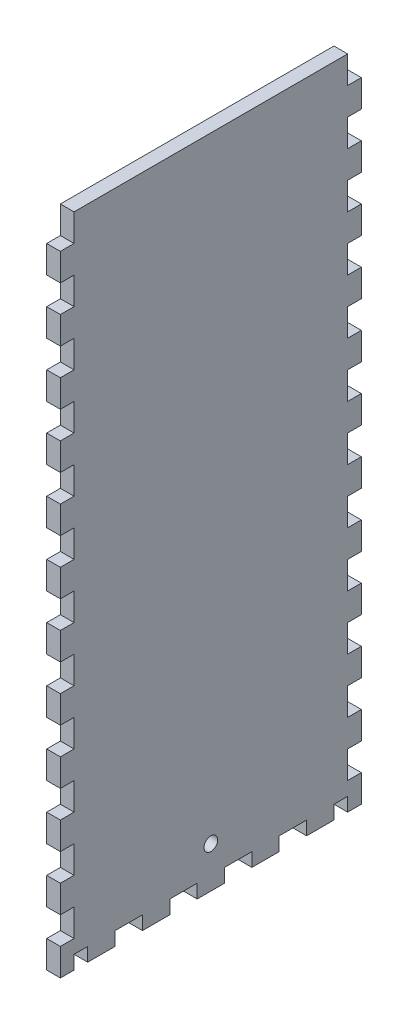
SolidWorks part; units mm, degrees
material "Acrylic (Medium-high impact)"
ref_plane "Front Plane" through (0, 0, 0) normal (0, 0, 1) x (1, 0, 0)
ref_plane "Top Plane" through (0, 0, 0) normal (0, 1, 0) x (1, 0, 0)
ref_plane "Right Plane" through (0, 0, 0) normal (1, 0, 0) x (0, 0, -1)
sketch "Sketch1" plane through (0, 0, 0) normal (0, 1, 0) x (1, 0, 0)
  line L1 (-136.525, 69.85) -> (136.525, 69.85)
  line L2 (-136.525, 69.85) -> (-136.525, -69.85)
  line L3 (-136.525, -69.85) -> (136.525, -69.85)
  line L4 (136.525, 69.85) -> (136.525, -69.85)
  point P4 (-136.525, 0)
  point P6 (0, 69.85)
  dimension "D1" = 139.7
  dimension "D2" = 273.05
extrude "Boss-Extrude1" add sketch "Sketch1" along normal blind 6.35
sketch "Sketch2" plane through (0, 6.35, 0) normal (0, 1, 0) x (1, 0, 0)
  line L0 (136.525, -69.85) -> (136.525, 69.85) construction
  line L1 (-136.525, 69.85) -> (136.525, 69.85)
  line L2 (-136.525, 69.85) -> (-136.525, -69.85)
  line L3 (-136.525, -69.85) -> (136.525, -69.85)
  line L4 (136.525, 69.85) -> (136.525, -69.85)
  line L5 (-136.525, -69.85) -> (136.525, -69.85) construction
  line L7 (-130.175, 63.5) -> (130.175, 63.5)
  line L8 (-130.175, 63.5) -> (-130.175, -63.5)
  line L9 (-130.175, -63.5) -> (130.175, -63.5)
  line L10 (130.175, 63.5) -> (130.175, -63.5)
  point P7 (-130.175, 0)
  point P14 (-136.525, 0)
  point P15 (0, -63.5)
  point P16 (0, -69.85)
  point P17 (130.175, 0)
  point P18 (136.525, 0)
  dimension "D1" = 6.35
  dimension "D2" = 6.35
extrude "Boss-Extrude2" add sketch "Sketch2" along normal blind 298.45
sketch "Sketch3" plane through (0, 0, 69.85) normal (0, 0, 1) x (1, 0, 0)
  line L0 (-25.273, 304.8) -> (-25.273, 0) construction
  line L2 (-130.175, 6.35) -> (130.175, 6.35) construction
  line L4 (-28.575, 283.21) -> (-28.575, 6.35)
  line L5 (-28.575, 6.35) -> (-21.971, 6.35)
  line L6 (-21.971, 292.354) -> (-21.971, 6.35)
  line L7 (-21.971, 292.354) -> (-41.529, 292.354)
  line L9 (-31.115, 285.75) -> (-41.529, 285.75)
  line L10 (-41.529, 292.354) -> (-41.529, 285.75)
  line L11 (-21.971, 101.6) -> (-9.271, 101.6) construction
  line L12 (-136.525, 0) -> (136.525, 0) construction
  line L13 (-12.446, 88.9) -> (-12.446, 101.6) construction
  line L14 (-15.621, 88.9) -> (-9.271, 88.9)
  line L15 (-15.621, 88.9) -> (-15.621, 71.9667)
  line L16 (-15.621, 71.9667) -> (-9.271, 71.9667)
  line L17 (-9.271, 88.9) -> (-9.271, 71.9667)
  line L18 (-15.621, 42.3333) -> (-9.271, 42.3333)
  line L19 (-15.621, 42.3333) -> (-15.621, 59.2667)
  line L20 (-15.621, 59.2667) -> (-9.271, 59.2667)
  line L21 (-9.271, 42.3333) -> (-9.271, 59.2667)
  line L26 (-15.621, 29.6333) -> (-9.271, 29.6333)
  line L27 (-15.621, 29.6333) -> (-15.621, 12.7)
  line L28 (-15.621, 12.7) -> (-9.271, 12.7)
  line L29 (-9.271, 29.6333) -> (-9.271, 12.7)
  line L30 (-12.446, 59.2667) -> (-12.446, 71.9667) construction
  line L31 (-12.446, 29.6333) -> (-12.446, 42.3333) construction
  line L32 (-12.446, 12.7) -> (-12.446, 0) construction
  line L33 (-136.525, 304.8) -> (136.525, 304.8) construction
  line L34 (-130.175, 304.8) -> (-130.175, 6.35) construction
  arc A0 (-28.575, 283.21) -> (-31.115, 285.75) centre (-31.115, 283.21) ccw
  point P5 (-25.273, 6.35)
  dimension "D5" = 2.54
  dimension "D1" = 6.604
  dimension "D2" = 12.954
  dimension "D3" = 6.604
  dimension "D4" = 286.004
  dimension "D6" = 101.6
  dimension "D7" = 12.7
  dimension "D8" = 12.7
  dimension "D9" = 6.35
  dimension "D10" = 101.6
extrude "Door Slot" cut sketch "Sketch3" against normal blind 12.7
sketch "Sketch4" plane through (0, 0, -63.5) normal (0, 0, 1) x (1, 0, 0)
  line L0 (-136.525, 304.8) -> (136.525, 304.8) construction
  line L1 (-47.879, 304.8) -> (-41.529, 304.8)
  line L2 (-47.879, 304.8) -> (-47.879, 6.35)
  line L3 (-47.879, 6.35) -> (-41.529, 6.35)
  line L4 (-41.529, 304.8) -> (-41.529, 6.35)
  line L5 (-18.796, 263.525) -> (-18.796, 247.65) construction
  line L6 (-41.529, 292.354) -> (-41.529, 285.75) construction
  line L7 (-21.971, 304.8) -> (-15.621, 304.8)
  line L8 (-21.971, 304.8) -> (-21.971, 6.35)
  line L9 (-21.971, 6.35) -> (-15.621, 6.35)
  line L10 (-15.621, 304.8) -> (-15.621, 6.35)
  line L11 (130.175, 6.35) -> (-130.175, 6.35) construction
  line L12 (-21.971, 6.35) -> (-21.971, 292.354) construction
  line L13 (-41.529, 304.8) -> (-47.879, 304.8)
  line L14 (-41.529, 304.8) -> (-41.529, 292.1)
  line L15 (-41.529, 292.1) -> (-47.879, 292.1)
  line L16 (-47.879, 304.8) -> (-47.879, 292.1)
  line L17 (-41.529, 276.225) -> (-47.879, 276.225)
  line L18 (-41.529, 276.225) -> (-41.529, 263.525)
  line L19 (-41.529, 263.525) -> (-47.879, 263.525)
  line L20 (-47.879, 276.225) -> (-47.879, 263.525)
  line L21 (-47.879, 6.35) -> (-41.529, 6.35)
  line L22 (-47.879, 6.35) -> (-47.879, 19.05)
  line L23 (-47.879, 19.05) -> (-41.529, 19.05)
  line L24 (-41.529, 6.35) -> (-41.529, 19.05)
  line L25 (-47.879, 34.925) -> (-41.529, 34.925)
  line L26 (-47.879, 34.925) -> (-47.879, 47.625)
  line L27 (-47.879, 47.625) -> (-41.529, 47.625)
  line L28 (-41.529, 34.925) -> (-41.529, 47.625)
  line L29 (-47.879, 92.075) -> (-41.529, 92.075)
  line L30 (-47.879, 92.075) -> (-47.879, 104.775)
  line L31 (-47.879, 104.775) -> (-41.529, 104.775)
  line L32 (-41.529, 92.075) -> (-41.529, 104.775)
  line L33 (-47.879, 149.225) -> (-41.529, 149.225)
  line L34 (-47.879, 149.225) -> (-47.879, 161.925)
  line L35 (-47.879, 161.925) -> (-41.529, 161.925)
  line L36 (-41.529, 149.225) -> (-41.529, 161.925)
  line L37 (-47.879, 177.8) -> (-41.529, 177.8)
  line L38 (-47.879, 177.8) -> (-47.879, 190.5)
  line L39 (-47.879, 190.5) -> (-41.529, 190.5)
  line L40 (-41.529, 177.8) -> (-41.529, 190.5)
  line L41 (-47.879, 206.375) -> (-41.529, 206.375)
  line L42 (-47.879, 206.375) -> (-47.879, 219.075)
  line L43 (-47.879, 219.075) -> (-41.529, 219.075)
  line L44 (-41.529, 206.375) -> (-41.529, 219.075)
  line L45 (-47.879, 234.95) -> (-41.529, 234.95)
  line L46 (-47.879, 234.95) -> (-47.879, 247.65)
  line L47 (-47.879, 247.65) -> (-41.529, 247.65)
  line L48 (-41.529, 234.95) -> (-41.529, 247.65)
  line L49 (-41.529, 133.35) -> (-47.879, 133.35)
  line L50 (-41.529, 133.35) -> (-41.529, 120.65)
  line L51 (-41.529, 120.65) -> (-47.879, 120.65)
  line L52 (-47.879, 133.35) -> (-47.879, 120.65)
  line L53 (-41.529, 76.2) -> (-47.879, 76.2)
  line L54 (-41.529, 76.2) -> (-41.529, 63.5)
  line L55 (-41.529, 63.5) -> (-47.879, 63.5)
  line L56 (-47.879, 76.2) -> (-47.879, 63.5)
  line L57 (-44.704, 304.8) -> (-44.704, 292.1) construction
  line L58 (-44.704, 292.1) -> (-44.704, 276.225) construction
  line L59 (-44.704, 276.225) -> (-44.704, 263.525) construction
  line L60 (-44.704, 247.65) -> (-44.704, 234.95) construction
  line L61 (-44.704, 234.95) -> (-44.704, 219.075) construction
  line L62 (-44.704, 219.075) -> (-44.704, 206.375) construction
  line L63 (-44.704, 206.375) -> (-44.704, 190.5) construction
  line L64 (-44.704, 190.5) -> (-44.704, 177.8) construction
  line L65 (-44.704, 177.8) -> (-44.704, 161.925) construction
  line L66 (-44.704, 161.925) -> (-44.704, 149.225) construction
  line L67 (-44.704, 133.35) -> (-44.704, 120.65) construction
  line L68 (-44.704, 120.65) -> (-44.704, 104.775) construction
  line L69 (-44.704, 104.775) -> (-44.704, 92.075) construction
  line L70 (-44.704, 92.075) -> (-44.704, 76.2) construction
  line L71 (-44.704, 76.2) -> (-44.704, 63.5) construction
  line L72 (-44.704, 63.5) -> (-44.704, 47.625) construction
  line L73 (-44.704, 47.625) -> (-44.704, 34.925) construction
  line L74 (-44.704, 34.925) -> (-44.704, 19.05) construction
  line L75 (-44.704, 19.05) -> (-44.704, 6.35) construction
  line L76 (-44.704, 149.225) -> (-44.704, 133.35) construction
  line L77 (-44.704, 263.525) -> (-44.704, 247.65) construction
  line L78 (-31.75, 304.8) -> (-31.75, 0) construction
  line L79 (136.525, 304.8) -> (-136.525, 304.8) construction
  line L80 (136.525, 0) -> (-136.525, 0) construction
  line L81 (-31.75, 8.3493) -> (-21.971, 8.3493) construction
  line L82 (-31.75, 8.3493) -> (-41.529, 8.3493) construction
  line L83 (-18.796, 149.225) -> (-18.796, 133.35) construction
  line L84 (-18.796, 19.05) -> (-18.796, 6.35) construction
  line L85 (-18.796, 34.925) -> (-18.796, 19.05) construction
  line L86 (-18.796, 47.625) -> (-18.796, 34.925) construction
  line L87 (-18.796, 63.5) -> (-18.796, 47.625) construction
  line L88 (-18.796, 76.2) -> (-18.796, 63.5) construction
  line L89 (-18.796, 92.075) -> (-18.796, 76.2) construction
  line L90 (-18.796, 104.775) -> (-18.796, 92.075) construction
  line L91 (-18.796, 120.65) -> (-18.796, 104.775) construction
  line L92 (-18.796, 133.35) -> (-18.796, 120.65) construction
  line L93 (-18.796, 161.925) -> (-18.796, 149.225) construction
  line L94 (-18.796, 177.8) -> (-18.796, 161.925) construction
  line L95 (-18.796, 190.5) -> (-18.796, 177.8) construction
  line L96 (-18.796, 206.375) -> (-18.796, 190.5) construction
  line L97 (-18.796, 219.075) -> (-18.796, 206.375) construction
  line L98 (-18.796, 234.95) -> (-18.796, 219.075) construction
  line L99 (-18.796, 247.65) -> (-18.796, 234.95) construction
  line L100 (-18.796, 276.225) -> (-18.796, 263.525) construction
  line L101 (-18.796, 292.1) -> (-18.796, 276.225) construction
  line L102 (-18.796, 304.8) -> (-18.796, 292.1) construction
  line L103 (-15.621, 76.2) -> (-15.621, 63.5)
  line L104 (-21.971, 63.5) -> (-15.621, 63.5)
  line L105 (-21.971, 76.2) -> (-21.971, 63.5)
  line L106 (-21.971, 76.2) -> (-15.621, 76.2)
  line L107 (-15.621, 133.35) -> (-15.621, 120.65)
  line L108 (-21.971, 120.65) -> (-15.621, 120.65)
  line L109 (-21.971, 133.35) -> (-21.971, 120.65)
  line L110 (-21.971, 133.35) -> (-15.621, 133.35)
  line L111 (-21.971, 234.95) -> (-21.971, 247.65)
  line L112 (-15.621, 247.65) -> (-21.971, 247.65)
  line L113 (-15.621, 234.95) -> (-15.621, 247.65)
  line L114 (-15.621, 234.95) -> (-21.971, 234.95)
  line L115 (-21.971, 206.375) -> (-21.971, 219.075)
  line L116 (-15.621, 219.075) -> (-21.971, 219.075)
  line L117 (-15.621, 206.375) -> (-15.621, 219.075)
  line L118 (-15.621, 206.375) -> (-21.971, 206.375)
  line L119 (-21.971, 177.8) -> (-21.971, 190.5)
  line L120 (-15.621, 190.5) -> (-21.971, 190.5)
  line L121 (-15.621, 177.8) -> (-15.621, 190.5)
  line L122 (-15.621, 177.8) -> (-21.971, 177.8)
  line L123 (-21.971, 149.225) -> (-21.971, 161.925)
  line L124 (-15.621, 161.925) -> (-21.971, 161.925)
  line L125 (-15.621, 149.225) -> (-15.621, 161.925)
  line L126 (-15.621, 149.225) -> (-21.971, 149.225)
  line L127 (-21.971, 92.075) -> (-21.971, 104.775)
  line L128 (-15.621, 104.775) -> (-21.971, 104.775)
  line L129 (-15.621, 92.075) -> (-15.621, 104.775)
  line L130 (-15.621, 92.075) -> (-21.971, 92.075)
  line L131 (-21.971, 34.925) -> (-21.971, 47.625)
  line L132 (-15.621, 47.625) -> (-21.971, 47.625)
  line L133 (-15.621, 34.925) -> (-15.621, 47.625)
  line L134 (-15.621, 34.925) -> (-21.971, 34.925)
  line L135 (-21.971, 6.35) -> (-21.971, 19.05)
  line L136 (-15.621, 19.05) -> (-21.971, 19.05)
  line L137 (-15.621, 6.35) -> (-15.621, 19.05)
  line L138 (-15.621, 6.35) -> (-21.971, 6.35)
  line L139 (-15.621, 276.225) -> (-15.621, 263.525)
  line L140 (-21.971, 263.525) -> (-15.621, 263.525)
  line L141 (-21.971, 276.225) -> (-21.971, 263.525)
  line L142 (-21.971, 276.225) -> (-15.621, 276.225)
  line L143 (-15.621, 304.8) -> (-15.621, 292.1)
  line L144 (-21.971, 292.1) -> (-15.621, 292.1)
  line L145 (-21.971, 304.8) -> (-21.971, 292.1)
  line L146 (-21.971, 304.8) -> (-15.621, 304.8)
  line L147 (-21.971, 304.8) -> (-21.971, 6.35)
  line L148 (-15.621, 6.35) -> (-21.971, 6.35)
  line L149 (-15.621, 304.8) -> (-15.621, 6.35)
  line L150 (-15.621, 304.8) -> (-21.971, 304.8)
  point P14 (-41.529, 289.052)
  dimension "D1" = 6.35
  dimension "D2" = 12.7
extrude "Door Guide Holes" cut sketch "Sketch4" against normal up to next contours L17 L4 L15 L2 | L2 L47 L4 L19 | L45 L2 L43 L4 | L41 L2 L39 L4 | L37 L2 L35 L4 | L49 L4 L33 L2 | L4 L51 L2 L31 | L53 L4 L29 L2 | L4 L55 L2 L27 | L25 L2 L23 L4
ref_plane "Plane1" through (-31.75, 0, 0) normal (-1, 0, 0) x (0, 0, 1)
mirror "Mirror1" about plane through (-31.75, 0, 0) normal (-1, 0, 0) of "Door Guide Holes"
sketch "Lever Holes" plane through (0, 0, 69.85) normal (0, 0, 1) x (1, 0, 0)
  line L0 (49.276, 31.75) -> (58.928, 31.75)
  line L1 (49.276, 31.75) -> (49.276, 25.4)
  line L2 (49.276, 25.4) -> (58.928, 25.4)
  line L3 (58.928, 31.75) -> (58.928, 25.4)
  line L4 (36.1315, 19.05) -> (42.4815, 19.05)
  line L5 (36.1315, 19.05) -> (36.1315, 12.7)
  line L6 (36.1315, 12.7) -> (42.4815, 12.7)
  line L7 (42.4815, 19.05) -> (42.4815, 12.7)
  line L8 (65.7225, 19.05) -> (72.0725, 19.05)
  line L9 (65.7225, 19.05) -> (65.7225, 12.7)
  line L10 (65.7225, 12.7) -> (72.0725, 12.7)
  line L11 (72.0725, 19.05) -> (72.0725, 12.7)
  line L12 (42.4815, 15.875) -> (65.7225, 15.875) construction
  line L13 (-136.525, 0) -> (136.525, 0) construction
  line L14 (-21.971, 6.35) -> (130.175, 6.35) construction
  line L15 (130.175, 6.35) -> (-130.175, 6.35) construction
  point P12 (54.102, 15.875)
  point P13 (54.102, 25.4)
  point P24 (54.102, 6.35)
  dimension "D1" = 9.652
  dimension "D2" = 6.35
  dimension "D3" = 6.35
  dimension "D4" = 6.35
  dimension "D5" = 23.241
  dimension "D6" = 25.4
  dimension "D7" = 12.7
extrude "Cut-Extrude1" cut sketch "Lever Holes" against normal through all
sketch "Sketch7" plane through (136.525, 0, 0) normal (1, 0, 0) x (0, 0, -1)
  line L0 (-37.211, 92.583) -> (37.211, 92.583)
  line L1 (-37.211, 92.583) -> (-37.211, 18.161)
  line L2 (-37.211, 18.161) -> (37.211, 18.161)
  line L3 (37.211, 92.583) -> (37.211, 18.161)
  line L4 (-69.85, 0) -> (69.85, 0) construction
  circle A0 centre (0, 55.372) radius 26.9875
  circle A1 centre (-37.211, 92.583) radius 3.175
  circle A2 centre (37.211, 92.583) radius 3.175
  circle A3 centre (-37.211, 18.161) radius 3.175
  circle A4 centre (37.211, 18.161) radius 3.175
  point P9 (0, 18.161)
  point P10 (-37.211, 55.372)
  dimension "D3" = 53.975
  dimension "D4" = 6.35
  dimension "D1" = 74.422
  dimension "D2" = 55.372
extrude "Cut-Extrude2" cut sketch "Sketch7" against normal up to next contours A0 | L0 A1 L1 | L1 A1 L0 | L3 A2 L0 | L0 A2 L3 | L2 A3 L1 | L1 A3 L2 | L2 A4 L3 | L3 A4 L2
sketch "Sketch8" plane through (-136.525, 0, 0) normal (-1, 0, 0) x (0, 0, 1)
  line L0 (-69.85, 0) -> (69.85, 0) construction
  circle A0 centre (0, 19.05) radius 3.175
  point P6 (0, 0)
  dimension "D1" = 6.35
  dimension "D2" = 19.05
extrude "Cut-Extrude3" cut sketch "Sketch8" against normal up to next
sketch "Bottom" plane through (0, 0, 0) normal (0, -1, 0) x (1, 0, 0)
  line L0 (-130.175, 63.5) -> (130.175, 63.5) construction
  line L1 (-136.525, 69.85) -> (-122.1539, 69.85)
  line L2 (-136.525, 69.85) -> (-136.525, 63.5)
  line L3 (-136.525, 63.5) -> (-122.1539, 63.5)
  line L4 (-122.1539, 69.85) -> (-122.1539, 63.5)
  line L5 (-122.1539, 69.85) -> (-107.7829, 69.85)
  line L6 (-122.1539, 69.85) -> (-122.1539, 63.5)
  line L7 (-122.1539, 63.5) -> (-107.7829, 63.5)
  line L8 (-107.7829, 69.85) -> (-107.7829, 63.5)
  line L9 (-107.7829, 69.85) -> (-93.4118, 69.85)
  line L10 (-107.7829, 69.85) -> (-107.7829, 63.5)
  line L11 (-107.7829, 63.5) -> (-93.4118, 63.5)
  line L12 (-93.4118, 69.85) -> (-93.4118, 63.5)
  line L13 (-93.4118, 69.85) -> (-79.0408, 69.85)
  line L14 (-93.4118, 69.85) -> (-93.4118, 63.5)
  line L15 (-93.4118, 63.5) -> (-79.0408, 63.5)
  line L16 (-79.0408, 69.85) -> (-79.0408, 63.5)
  line L17 (-136.525, 69.85) -> (136.525, 69.85) construction
  line L18 (-41.529, 63.5) -> (-21.971, 63.5) construction
  line L19 (-79.0408, 69.85) -> (-64.6697, 69.85)
  line L20 (-79.0408, 69.85) -> (-79.0408, 63.5)
  line L21 (-79.0408, 63.5) -> (-64.6697, 63.5)
  line L22 (-64.6697, 69.85) -> (-64.6697, 63.5)
  line L23 (-64.6697, 69.85) -> (-50.2987, 69.85)
  line L24 (-64.6697, 69.85) -> (-64.6697, 63.5)
  line L25 (-64.6697, 63.5) -> (-50.2987, 63.5)
  line L26 (-50.2987, 69.85) -> (-50.2987, 63.5)
  line L27 (-50.2987, 69.85) -> (-35.9276, 69.85)
  line L28 (-50.2987, 69.85) -> (-50.2987, 63.5)
  line L29 (-50.2987, 63.5) -> (-35.9276, 63.5)
  line L30 (-35.9276, 69.85) -> (-35.9276, 63.5)
  line L31 (-35.9276, 69.85) -> (-21.5566, 69.85)
  line L32 (-35.9276, 69.85) -> (-35.9276, 63.5)
  line L33 (-35.9276, 63.5) -> (-21.5566, 63.5)
  line L34 (-21.5566, 69.85) -> (-21.5566, 63.5)
  line L36 (-21.5566, 69.85) -> (-7.1855, 69.85)
  line L37 (-21.5566, 69.85) -> (-21.5566, 63.5)
  line L38 (-21.5566, 63.5) -> (-7.1855, 63.5)
  line L39 (-7.1855, 69.85) -> (-7.1855, 63.5)
  line L40 (-7.1855, 69.85) -> (7.1855, 69.85)
  line L41 (-7.1855, 69.85) -> (-7.1855, 63.5)
  line L42 (-7.1855, 63.5) -> (7.1855, 63.5)
  line L43 (7.1855, 69.85) -> (7.1855, 63.5)
  line L44 (7.1855, 69.85) -> (21.5566, 69.85)
  line L45 (7.1855, 69.85) -> (7.1855, 63.5)
  line L46 (7.1855, 63.5) -> (21.5566, 63.5)
  line L47 (21.5566, 69.85) -> (21.5566, 63.5)
  line L48 (21.5566, 69.85) -> (35.9276, 69.85)
  line L49 (21.5566, 69.85) -> (21.5566, 63.5)
  line L50 (21.5566, 63.5) -> (35.9276, 63.5)
  line L51 (35.9276, 69.85) -> (35.9276, 63.5)
  line L52 (35.9276, 69.85) -> (50.2987, 69.85)
  line L53 (35.9276, 69.85) -> (35.9276, 63.5)
  line L54 (35.9276, 63.5) -> (50.2987, 63.5)
  line L55 (50.2987, 69.85) -> (50.2987, 63.5)
  line L56 (50.2987, 69.85) -> (64.6697, 69.85)
  line L57 (50.2987, 69.85) -> (50.2987, 63.5)
  line L58 (50.2987, 63.5) -> (64.6697, 63.5)
  line L59 (64.6697, 69.85) -> (64.6697, 63.5)
  line L60 (64.6697, 69.85) -> (79.0408, 69.85)
  line L61 (64.6697, 69.85) -> (64.6697, 63.5)
  line L62 (64.6697, 63.5) -> (79.0408, 63.5)
  line L63 (79.0408, 69.85) -> (79.0408, 63.5)
  line L64 (79.0408, 69.85) -> (93.4118, 69.85)
  line L65 (79.0408, 69.85) -> (79.0408, 63.5)
  line L66 (79.0408, 63.5) -> (93.4118, 63.5)
  line L67 (93.4118, 69.85) -> (93.4118, 63.5)
  line L68 (93.4118, 69.85) -> (107.7829, 69.85)
  line L69 (93.4118, 69.85) -> (93.4118, 63.5)
  line L70 (93.4118, 63.5) -> (107.7829, 63.5)
  line L71 (107.7829, 69.85) -> (107.7829, 63.5)
  line L72 (107.7829, 69.85) -> (122.1539, 69.85)
  line L73 (107.7829, 69.85) -> (107.7829, 63.5)
  line L74 (107.7829, 63.5) -> (122.1539, 63.5)
  line L75 (122.1539, 69.85) -> (122.1539, 63.5)
  line L76 (-130.175, -63.5) -> (-130.175, 63.5) construction
  line L77 (-136.525, 69.85) -> (-130.175, 69.85)
  line L78 (-136.525, 69.85) -> (-136.525, 57.15)
  line L79 (-136.525, 57.15) -> (-130.175, 57.15)
  line L80 (-130.175, 69.85) -> (-130.175, 57.15)
  line L82 (-136.525, 57.15) -> (-130.175, 57.15)
  line L83 (-136.525, 57.15) -> (-136.525, 44.45)
  line L84 (-136.525, 44.45) -> (-130.175, 44.45)
  line L85 (-130.175, 57.15) -> (-130.175, 44.45)
  line L86 (-136.525, 44.45) -> (-130.175, 44.45)
  line L87 (-136.525, 44.45) -> (-136.525, 31.75)
  line L88 (-136.525, 31.75) -> (-130.175, 31.75)
  line L89 (-130.175, 44.45) -> (-130.175, 31.75)
  line L90 (-136.525, 31.75) -> (-130.175, 31.75)
  line L91 (-136.525, 31.75) -> (-136.525, 19.05)
  line L92 (-136.525, 19.05) -> (-130.175, 19.05)
  line L93 (-130.175, 31.75) -> (-130.175, 19.05)
  line L94 (-136.525, 19.05) -> (-130.175, 19.05)
  line L95 (-136.525, 19.05) -> (-136.525, 6.35)
  line L96 (-136.525, 6.35) -> (-130.175, 6.35)
  line L97 (-130.175, 19.05) -> (-130.175, 6.35)
  line L98 (-136.525, 6.35) -> (-130.175, 6.35)
  line L99 (-136.525, 6.35) -> (-136.525, -6.35)
  line L100 (-136.525, -6.35) -> (-130.175, -6.35)
  line L101 (-130.175, 6.35) -> (-130.175, -6.35)
  line L102 (-136.525, -6.35) -> (-130.175, -6.35)
  line L103 (-136.525, -6.35) -> (-136.525, -19.05)
  line L104 (-136.525, -19.05) -> (-130.175, -19.05)
  line L105 (-130.175, -6.35) -> (-130.175, -19.05)
  line L106 (-136.525, -19.05) -> (-130.175, -19.05)
  line L107 (-136.525, -19.05) -> (-136.525, -31.75)
  line L108 (-136.525, -31.75) -> (-130.175, -31.75)
  line L109 (-130.175, -19.05) -> (-130.175, -31.75)
  line L110 (-136.525, -31.75) -> (-130.175, -31.75)
  line L111 (-136.525, -31.75) -> (-136.525, -44.45)
  line L112 (-136.525, -44.45) -> (-130.175, -44.45)
  line L113 (-130.175, -31.75) -> (-130.175, -44.45)
  line L114 (-136.525, -44.45) -> (-130.175, -44.45)
  line L115 (-136.525, -44.45) -> (-136.525, -57.15)
  line L116 (-136.525, -57.15) -> (-130.175, -57.15)
  line L117 (-130.175, -44.45) -> (-130.175, -57.15)
  line L118 (136.525, 69.85) -> (136.525, -69.85) construction
  line L119 (122.1539, 69.85) -> (136.525, 69.85)
  line L120 (122.1539, 69.85) -> (122.1539, 63.5)
  line L121 (122.1539, 63.5) -> (136.525, 63.5)
  line L122 (136.525, 69.85) -> (136.525, 63.5)
  line L123 (136.525, -69.85) -> (-136.525, -69.85) construction
  line L124 (-136.525, -57.15) -> (-130.175, -57.15)
  line L125 (-136.525, -57.15) -> (-136.525, -69.85)
  line L126 (-136.525, -69.85) -> (-130.175, -69.85)
  line L127 (-130.175, -57.15) -> (-130.175, -69.85)
  line L128 (150.1775, 0) -> (-150.1775, 0) construction
  line L129 (136.525, -69.85) -> (136.525, -63.5)
  line L130 (122.1539, -63.5) -> (136.525, -63.5)
  line L131 (122.1539, -69.85) -> (136.525, -69.85)
  line L132 (122.1539, -69.85) -> (122.1539, -63.5)
  line L133 (107.7829, -63.5) -> (122.1539, -63.5)
  line L134 (107.7829, -69.85) -> (122.1539, -69.85)
  line L135 (107.7829, -69.85) -> (107.7829, -63.5)
  line L136 (93.4118, -63.5) -> (107.7829, -63.5)
  line L137 (93.4118, -69.85) -> (107.7829, -69.85)
  line L138 (93.4118, -69.85) -> (93.4118, -63.5)
  line L139 (79.0408, -63.5) -> (93.4118, -63.5)
  line L140 (79.0408, -69.85) -> (93.4118, -69.85)
  line L141 (79.0408, -69.85) -> (79.0408, -63.5)
  line L142 (64.6697, -63.5) -> (79.0408, -63.5)
  line L143 (64.6697, -69.85) -> (79.0408, -69.85)
  line L144 (50.2987, -63.5) -> (64.6697, -63.5)
  line L145 (64.6697, -69.85) -> (64.6697, -63.5)
  line L146 (50.2987, -69.85) -> (64.6697, -69.85)
  line L147 (50.2987, -69.85) -> (50.2987, -63.5)
  line L148 (35.9276, -63.5) -> (50.2987, -63.5)
  line L149 (35.9276, -69.85) -> (50.2987, -69.85)
  line L150 (35.9276, -69.85) -> (35.9276, -63.5)
  line L151 (21.5566, -63.5) -> (35.9276, -63.5)
  line L152 (21.5566, -69.85) -> (35.9276, -69.85)
  line L153 (21.5566, -69.85) -> (21.5566, -63.5)
  line L154 (7.1855, -69.85) -> (21.5566, -69.85)
  line L155 (7.1855, -63.5) -> (21.5566, -63.5)
  line L156 (7.1855, -69.85) -> (7.1855, -63.5)
  line L157 (-7.1855, -63.5) -> (7.1855, -63.5)
  line L158 (-7.1855, -69.85) -> (7.1855, -69.85)
  line L159 (-21.5566, -63.5) -> (-7.1855, -63.5)
  line L160 (-7.1855, -69.85) -> (-7.1855, -63.5)
  line L161 (-21.5566, -69.85) -> (-7.1855, -69.85)
  line L162 (-21.5566, -69.85) -> (-21.5566, -63.5)
  line L163 (-35.9276, -63.5) -> (-21.5566, -63.5)
  line L164 (-35.9276, -69.85) -> (-21.5566, -69.85)
  line L165 (-35.9276, -69.85) -> (-35.9276, -63.5)
  line L166 (-50.2987, -63.5) -> (-35.9276, -63.5)
  line L167 (-50.2987, -69.85) -> (-35.9276, -69.85)
  line L168 (-50.2987, -69.85) -> (-50.2987, -63.5)
  line L169 (-64.6697, -69.85) -> (-50.2987, -69.85)
  line L170 (-64.6697, -63.5) -> (-50.2987, -63.5)
  line L171 (-79.0408, -63.5) -> (-64.6697, -63.5)
  line L172 (-64.6697, -69.85) -> (-64.6697, -63.5)
  line L173 (-79.0408, -69.85) -> (-64.6697, -69.85)
  line L174 (-93.4118, -69.85) -> (-79.0408, -69.85)
  line L175 (-93.4118, -63.5) -> (-79.0408, -63.5)
  line L176 (-79.0408, -69.85) -> (-79.0408, -63.5)
  line L177 (-107.7829, -69.85) -> (-107.7829, -63.5)
  line L178 (-107.7829, -69.85) -> (-93.4118, -69.85)
  line L179 (-93.4118, -69.85) -> (-93.4118, -63.5)
  line L180 (-107.7829, -63.5) -> (-93.4118, -63.5)
  line L181 (-122.1539, -63.5) -> (-107.7829, -63.5)
  line L182 (-122.1539, -69.85) -> (-107.7829, -69.85)
  line L183 (-122.1539, -69.85) -> (-122.1539, -63.5)
  line L184 (-136.525, -69.85) -> (-122.1539, -69.85)
  line L185 (-136.525, -69.85) -> (-136.525, -63.5)
  line L186 (-136.525, -63.5) -> (-122.1539, -63.5)
  line L187 (0, -76.835) -> (0, 76.835) construction
  line L188 (136.525, -69.85) -> (130.175, -69.85)
  line L189 (130.175, -57.15) -> (130.175, -69.85)
  line L190 (136.525, -57.15) -> (136.525, -69.85)
  line L191 (136.525, -57.15) -> (130.175, -57.15)
  line L192 (130.175, -44.45) -> (130.175, -57.15)
  line L193 (136.525, -44.45) -> (136.525, -57.15)
  line L194 (136.525, -44.45) -> (130.175, -44.45)
  line L195 (130.175, -31.75) -> (130.175, -44.45)
  line L196 (136.525, -31.75) -> (136.525, -44.45)
  line L197 (136.525, -31.75) -> (130.175, -31.75)
  line L198 (136.525, -19.05) -> (136.525, -31.75)
  line L199 (130.175, -19.05) -> (130.175, -31.75)
  line L200 (130.175, -6.35) -> (130.175, -19.05)
  line L201 (136.525, -6.35) -> (136.525, -19.05)
  line L202 (136.525, -19.05) -> (130.175, -19.05)
  line L203 (136.525, -6.35) -> (130.175, -6.35)
  line L204 (130.175, 6.35) -> (130.175, -6.35)
  line L205 (136.525, 6.35) -> (136.525, -6.35)
  line L206 (136.525, 6.35) -> (130.175, 6.35)
  line L207 (130.175, 19.05) -> (130.175, 6.35)
  line L208 (136.525, 19.05) -> (136.525, 6.35)
  line L209 (136.525, 19.05) -> (130.175, 19.05)
  line L210 (136.525, 31.75) -> (130.175, 31.75)
  line L211 (136.525, 44.45) -> (130.175, 44.45)
  line L212 (136.525, 57.15) -> (130.175, 57.15)
  line L213 (130.175, 31.75) -> (130.175, 19.05)
  line L214 (136.525, 31.75) -> (136.525, 19.05)
  line L215 (130.175, 44.45) -> (130.175, 31.75)
  line L216 (136.525, 44.45) -> (136.525, 31.75)
  line L217 (130.175, 57.15) -> (130.175, 44.45)
  line L218 (136.525, 57.15) -> (136.525, 44.45)
  line L219 (130.175, 69.85) -> (130.175, 57.15)
  line L220 (136.525, 69.85) -> (136.525, 57.15)
sketch "Front/Back" plane through (0, 0, 69.85) normal (0, 0, 1) x (1, 0, 0)
  line L0 (-130.175, 6.35) -> (-28.575, 6.35) construction
  line L1 (-136.525, 0) -> (-122.1539, 0)
  line L2 (-136.525, 0) -> (-136.525, 6.35)
  line L3 (-136.525, 6.35) -> (-122.1539, 6.35)
  line L4 (-122.1539, 0) -> (-122.1539, 6.35)
  line L5 (-136.525, 0) -> (136.525, 0) construction
  line L6 (-107.7829, 0) -> (-93.4118, 0) construction
  line L7 (-122.1539, 6.35) -> (-107.7829, 6.35)
  line L8 (-122.1539, 6.35) -> (-122.1539, 0)
  line L9 (-122.1539, 0) -> (-107.7829, 0)
  line L10 (-107.7829, 6.35) -> (-107.7829, 0)
  line L11 (-79.0408, 0) -> (-64.6697, 0) construction
  line L12 (-107.7829, 6.35) -> (-93.4118, 6.35)
  line L13 (-107.7829, 6.35) -> (-107.7829, 0)
  line L14 (-107.7829, 0) -> (-93.4118, 0)
  line L15 (-93.4118, 6.35) -> (-93.4118, 0)
  line L16 (-93.4118, 6.35) -> (-79.0408, 6.35)
  line L17 (-93.4118, 6.35) -> (-93.4118, 0)
  line L18 (-93.4118, 0) -> (-79.0408, 0)
  line L19 (-79.0408, 6.35) -> (-79.0408, 0)
  line L20 (-64.6697, 0) -> (-50.2987, 0) construction
  line L21 (-79.0408, 6.35) -> (-64.6697, 6.35)
  line L22 (-79.0408, 6.35) -> (-79.0408, 0)
  line L23 (-79.0408, 0) -> (-64.6697, 0)
  line L24 (-64.6697, 6.35) -> (-64.6697, 0)
  line L25 (-64.6697, 6.35) -> (-50.2987, 6.35)
  line L26 (-64.6697, 6.35) -> (-64.6697, 0)
  line L27 (-64.6697, 0) -> (-50.2987, 0)
  line L28 (-50.2987, 6.35) -> (-50.2987, 0)
  line L29 (-50.2987, 0) -> (-35.9276, 0) construction
  line L30 (-50.2987, 6.35) -> (-35.9276, 6.35)
  line L31 (-50.2987, 6.35) -> (-50.2987, 0)
  line L32 (-50.2987, 0) -> (-35.9276, 0)
  line L33 (-35.9276, 6.35) -> (-35.9276, 0)
  line L34 (-21.5566, 0) -> (-7.1855, 0) construction
  line L35 (-35.9276, 6.35) -> (-21.5566, 6.35)
  line L36 (-35.9276, 6.35) -> (-35.9276, 0)
  line L37 (-35.9276, 0) -> (-21.5566, 0)
  line L38 (-21.5566, 6.35) -> (-21.5566, 0)
  line L39 (7.1855, 0) -> (21.5566, 0) construction
  line L40 (-21.5566, 6.35) -> (-7.1855, 6.35)
  line L41 (-21.5566, 6.35) -> (-21.5566, 0)
  line L42 (-21.5566, 0) -> (-7.1855, 0)
  line L43 (-7.1855, 6.35) -> (-7.1855, 0)
  line L44 (-7.1855, 6.35) -> (7.1855, 6.35)
  line L45 (-7.1855, 6.35) -> (-7.1855, 0)
  line L46 (-7.1855, 0) -> (7.1855, 0)
  line L47 (7.1855, 6.35) -> (7.1855, 0)
  line L48 (7.1855, 0) -> (21.5566, 0) construction
  line L49 (35.9276, 0) -> (50.2987, 0) construction
  line L50 (7.1855, 6.35) -> (21.5566, 6.35)
  line L51 (7.1855, 6.35) -> (7.1855, 0)
  line L52 (7.1855, 0) -> (21.5566, 0)
  line L53 (21.5566, 6.35) -> (21.5566, 0)
  line L54 (21.5566, 6.35) -> (35.9276, 6.35)
  line L55 (21.5566, 6.35) -> (21.5566, 0)
  line L56 (21.5566, 0) -> (35.9276, 0)
  line L57 (35.9276, 6.35) -> (35.9276, 0)
  line L58 (64.6697, 0) -> (79.0408, 0) construction
  line L59 (35.9276, 6.35) -> (50.2987, 6.35)
  line L60 (35.9276, 6.35) -> (35.9276, 0)
  line L61 (35.9276, 0) -> (50.2987, 0)
  line L62 (50.2987, 6.35) -> (50.2987, 0)
  line L63 (50.2987, 6.35) -> (64.6697, 6.35)
  line L64 (50.2987, 6.35) -> (50.2987, 0)
  line L65 (50.2987, 0) -> (64.6697, 0)
  line L66 (64.6697, 6.35) -> (64.6697, 0)
  line L67 (50.2987, 0) -> (64.6697, 0) construction
  line L68 (93.4118, 0) -> (107.7829, 0) construction
  line L69 (64.6697, 6.35) -> (79.0408, 6.35)
  line L70 (64.6697, 6.35) -> (64.6697, 0)
  line L71 (64.6697, 0) -> (79.0408, 0)
  line L72 (79.0408, 6.35) -> (79.0408, 0)
  line L73 (79.0408, 6.35) -> (93.4118, 6.35)
  line L74 (79.0408, 6.35) -> (79.0408, 0)
  line L75 (79.0408, 0) -> (93.4118, 0)
  line L76 (93.4118, 6.35) -> (93.4118, 0)
  line L77 (107.7829, 0) -> (122.1539, 0) construction
  line L78 (93.4118, 6.35) -> (107.7829, 6.35)
  line L79 (93.4118, 6.35) -> (93.4118, 0)
  line L80 (93.4118, 0) -> (107.7829, 0)
  line L81 (107.7829, 6.35) -> (107.7829, 0)
  line L82 (107.7829, 0) -> (122.1539, 0) construction
  line L84 (107.7829, 6.35) -> (122.1539, 6.35)
  line L85 (107.7829, 6.35) -> (107.7829, 0)
  line L86 (107.7829, 0) -> (122.1539, 0)
  line L87 (122.1539, 6.35) -> (122.1539, 0)
  line L88 (122.1539, 6.35) -> (136.525, 6.35)
  line L89 (122.1539, 6.35) -> (122.1539, 0)
  line L90 (122.1539, 0) -> (136.525, 0)
  line L91 (136.525, 6.35) -> (136.525, 0)
  line L92 (-130.175, 304.8) -> (-130.175, 6.35) construction
  line L93 (-136.525, 0) -> (-130.175, 0)
  line L94 (-136.525, 0) -> (-136.525, 12.7)
  line L95 (-136.525, 12.7) -> (-130.175, 12.7)
  line L96 (-130.175, 0) -> (-130.175, 12.7)
  line L97 (-136.525, 304.8) -> (-136.525, 0) construction
  line L98 (-136.525, 12.7) -> (-130.175, 12.7)
  line L99 (-136.525, 12.7) -> (-136.525, 25.4)
  line L100 (-136.525, 25.4) -> (-130.175, 25.4)
  line L101 (-130.175, 12.7) -> (-130.175, 25.4)
  line L102 (-136.525, 25.4) -> (-130.175, 25.4)
  line L103 (-136.525, 25.4) -> (-136.525, 38.1)
  line L104 (-136.525, 38.1) -> (-130.175, 38.1)
  line L105 (-130.175, 25.4) -> (-130.175, 38.1)
  line L106 (-136.525, 38.1) -> (-130.175, 38.1)
  line L107 (-136.525, 38.1) -> (-136.525, 50.8)
  line L108 (-136.525, 50.8) -> (-130.175, 50.8)
  line L109 (-130.175, 38.1) -> (-130.175, 50.8)
  line L110 (-136.525, 50.8) -> (-130.175, 50.8)
  line L111 (-136.525, 50.8) -> (-136.525, 63.5)
  line L112 (-136.525, 63.5) -> (-130.175, 63.5)
  line L113 (-130.175, 50.8) -> (-130.175, 63.5)
  line L114 (-136.525, 63.5) -> (-130.175, 63.5)
  line L115 (-136.525, 63.5) -> (-136.525, 76.2)
  line L116 (-136.525, 76.2) -> (-130.175, 76.2)
  line L117 (-130.175, 63.5) -> (-130.175, 76.2)
  line L118 (-136.525, 76.2) -> (-130.175, 76.2)
  line L119 (-136.525, 76.2) -> (-136.525, 88.9)
  line L120 (-136.525, 88.9) -> (-130.175, 88.9)
  line L121 (-130.175, 76.2) -> (-130.175, 88.9)
  line L122 (-136.525, 88.9) -> (-130.175, 88.9)
  line L123 (-136.525, 88.9) -> (-136.525, 101.6)
  line L124 (-136.525, 101.6) -> (-130.175, 101.6)
  line L125 (-130.175, 88.9) -> (-130.175, 101.6)
  line L126 (-136.525, 101.6) -> (-130.175, 101.6)
  line L127 (-136.525, 101.6) -> (-136.525, 114.3)
  line L128 (-136.525, 114.3) -> (-130.175, 114.3)
  line L129 (-130.175, 101.6) -> (-130.175, 114.3)
  line L130 (-136.525, 114.3) -> (-130.175, 114.3)
  line L131 (-136.525, 114.3) -> (-136.525, 127)
  line L132 (-136.525, 127) -> (-130.175, 127)
  line L133 (-130.175, 114.3) -> (-130.175, 127)
  line L134 (-136.525, 127) -> (-130.175, 127)
  line L135 (-136.525, 127) -> (-136.525, 139.7)
  line L136 (-136.525, 139.7) -> (-130.175, 139.7)
  line L137 (-130.175, 127) -> (-130.175, 139.7)
  line L138 (-136.525, 139.7) -> (-130.175, 139.7)
  line L139 (-136.525, 139.7) -> (-136.525, 152.4)
  line L140 (-136.525, 152.4) -> (-130.175, 152.4)
  line L141 (-130.175, 139.7) -> (-130.175, 152.4)
  line L142 (-136.525, 152.4) -> (-130.175, 152.4)
  line L143 (-136.525, 152.4) -> (-136.525, 165.1)
  line L144 (-136.525, 165.1) -> (-130.175, 165.1)
  line L145 (-130.175, 152.4) -> (-130.175, 165.1)
  line L146 (-136.525, 165.1) -> (-130.175, 165.1)
  line L147 (-136.525, 165.1) -> (-136.525, 177.8)
  line L148 (-136.525, 177.8) -> (-130.175, 177.8)
  line L149 (-130.175, 165.1) -> (-130.175, 177.8)
  line L150 (-136.525, 177.8) -> (-130.175, 177.8)
  line L151 (-136.525, 177.8) -> (-136.525, 190.5)
  line L152 (-136.525, 190.5) -> (-130.175, 190.5)
  line L153 (-130.175, 177.8) -> (-130.175, 190.5)
  line L154 (-136.525, 190.5) -> (-130.175, 190.5)
  line L155 (-136.525, 190.5) -> (-136.525, 203.2)
  line L156 (-136.525, 203.2) -> (-130.175, 203.2)
  line L157 (-130.175, 190.5) -> (-130.175, 203.2)
  line L158 (-136.525, 203.2) -> (-130.175, 203.2)
  line L159 (-136.525, 203.2) -> (-136.525, 215.9)
  line L160 (-136.525, 215.9) -> (-130.175, 215.9)
  line L161 (-130.175, 203.2) -> (-130.175, 215.9)
  line L162 (-136.525, 215.9) -> (-130.175, 215.9)
  line L163 (-136.525, 215.9) -> (-136.525, 228.6)
  line L164 (-136.525, 228.6) -> (-130.175, 228.6)
  line L165 (-130.175, 215.9) -> (-130.175, 228.6)
  line L166 (-136.525, 228.6) -> (-130.175, 228.6)
  line L167 (-136.525, 228.6) -> (-136.525, 241.3)
  line L168 (-136.525, 241.3) -> (-130.175, 241.3)
  line L169 (-130.175, 228.6) -> (-130.175, 241.3)
  line L170 (-136.525, 241.3) -> (-130.175, 241.3)
  line L171 (-136.525, 241.3) -> (-136.525, 254)
  line L172 (-136.525, 254) -> (-130.175, 254)
  line L173 (-130.175, 241.3) -> (-130.175, 254)
  line L174 (-136.525, 254) -> (-130.175, 254)
  line L175 (-136.525, 254) -> (-136.525, 266.7)
  line L176 (-136.525, 266.7) -> (-130.175, 266.7)
  line L177 (-130.175, 254) -> (-130.175, 266.7)
  line L178 (-136.525, 266.7) -> (-130.175, 266.7)
  line L179 (-136.525, 266.7) -> (-136.525, 279.4)
  line L180 (-136.525, 279.4) -> (-130.175, 279.4)
  line L181 (-130.175, 266.7) -> (-130.175, 279.4)
  line L182 (-136.525, 279.4) -> (-130.175, 279.4)
  line L183 (-136.525, 279.4) -> (-136.525, 292.1)
  line L184 (-136.525, 292.1) -> (-130.175, 292.1)
  line L185 (-130.175, 279.4) -> (-130.175, 292.1)
  line L186 (-136.525, 292.1) -> (-130.175, 292.1)
  line L187 (-136.525, 292.1) -> (-136.525, 304.8)
  line L188 (-136.525, 304.8) -> (-130.175, 304.8)
  line L189 (-130.175, 292.1) -> (-130.175, 304.8)
  line L190 (-136.525, 304.8) -> (-130.175, 304.8)
  line L194 (-136.525, 304.8) -> (136.525, 304.8) construction
  line L195 (0, -76.835) -> (0, 76.835) construction
  line L196 (136.525, 304.8) -> (130.175, 304.8)
  line L197 (130.175, 292.1) -> (130.175, 304.8)
  line L198 (136.525, 304.8) -> (130.175, 304.8)
  line L199 (136.525, 292.1) -> (136.525, 304.8)
  line L200 (136.525, 292.1) -> (130.175, 292.1)
  line L201 (130.175, 279.4) -> (130.175, 292.1)
  line L202 (136.525, 292.1) -> (130.175, 292.1)
  line L203 (136.525, 279.4) -> (136.525, 292.1)
  line L204 (136.525, 279.4) -> (130.175, 279.4)
  line L205 (130.175, 266.7) -> (130.175, 279.4)
  line L206 (136.525, 279.4) -> (130.175, 279.4)
  line L207 (136.525, 266.7) -> (136.525, 279.4)
  line L208 (136.525, 266.7) -> (130.175, 266.7)
  line L209 (130.175, 254) -> (130.175, 266.7)
  line L210 (136.525, 266.7) -> (130.175, 266.7)
  line L211 (136.525, 254) -> (136.525, 266.7)
  line L212 (136.525, 254) -> (130.175, 254)
  line L213 (130.175, 241.3) -> (130.175, 254)
  line L214 (136.525, 254) -> (130.175, 254)
  line L215 (136.525, 241.3) -> (136.525, 254)
  line L216 (136.525, 241.3) -> (130.175, 241.3)
  line L217 (130.175, 228.6) -> (130.175, 241.3)
  line L218 (136.525, 241.3) -> (130.175, 241.3)
  line L219 (136.525, 228.6) -> (136.525, 241.3)
  line L220 (136.525, 228.6) -> (130.175, 228.6)
  line L221 (130.175, 215.9) -> (130.175, 228.6)
  line L222 (136.525, 228.6) -> (130.175, 228.6)
  line L223 (136.525, 215.9) -> (136.525, 228.6)
  line L224 (136.525, 215.9) -> (130.175, 215.9)
  line L225 (130.175, 203.2) -> (130.175, 215.9)
  line L226 (136.525, 215.9) -> (130.175, 215.9)
  line L227 (136.525, 203.2) -> (136.525, 215.9)
  line L228 (136.525, 203.2) -> (130.175, 203.2)
  line L229 (130.175, 190.5) -> (130.175, 203.2)
  line L230 (136.525, 203.2) -> (130.175, 203.2)
  line L231 (136.525, 190.5) -> (136.525, 203.2)
  line L232 (136.525, 190.5) -> (130.175, 190.5)
  line L233 (130.175, 177.8) -> (130.175, 190.5)
  line L234 (136.525, 190.5) -> (130.175, 190.5)
  line L235 (136.525, 177.8) -> (136.525, 190.5)
  line L236 (136.525, 177.8) -> (130.175, 177.8)
  line L237 (130.175, 165.1) -> (130.175, 177.8)
  line L238 (136.525, 177.8) -> (130.175, 177.8)
  line L239 (136.525, 165.1) -> (136.525, 177.8)
  line L240 (136.525, 165.1) -> (130.175, 165.1)
  line L241 (130.175, 152.4) -> (130.175, 165.1)
  line L242 (136.525, 165.1) -> (130.175, 165.1)
  line L243 (136.525, 152.4) -> (136.525, 165.1)
  line L244 (136.525, 152.4) -> (130.175, 152.4)
  line L245 (130.175, 139.7) -> (130.175, 152.4)
  line L246 (136.525, 152.4) -> (130.175, 152.4)
  line L247 (136.525, 139.7) -> (136.525, 152.4)
  line L248 (136.525, 139.7) -> (130.175, 139.7)
  line L249 (130.175, 127) -> (130.175, 139.7)
  line L250 (136.525, 139.7) -> (130.175, 139.7)
  line L251 (136.525, 127) -> (136.525, 139.7)
  line L252 (136.525, 127) -> (130.175, 127)
  line L253 (130.175, 114.3) -> (130.175, 127)
  line L254 (136.525, 127) -> (130.175, 127)
  line L255 (136.525, 114.3) -> (136.525, 127)
  line L256 (136.525, 114.3) -> (130.175, 114.3)
  line L257 (130.175, 101.6) -> (130.175, 114.3)
  line L258 (136.525, 114.3) -> (130.175, 114.3)
  line L259 (136.525, 101.6) -> (136.525, 114.3)
  line L260 (136.525, 101.6) -> (130.175, 101.6)
  line L261 (130.175, 88.9) -> (130.175, 101.6)
  line L262 (136.525, 101.6) -> (130.175, 101.6)
  line L263 (136.525, 88.9) -> (136.525, 101.6)
  line L264 (136.525, 88.9) -> (130.175, 88.9)
  line L265 (130.175, 76.2) -> (130.175, 88.9)
  line L266 (136.525, 88.9) -> (130.175, 88.9)
  line L267 (136.525, 76.2) -> (136.525, 88.9)
  line L268 (136.525, 76.2) -> (130.175, 76.2)
  line L269 (130.175, 63.5) -> (130.175, 76.2)
  line L270 (136.525, 76.2) -> (130.175, 76.2)
  line L271 (136.525, 63.5) -> (136.525, 76.2)
  line L272 (136.525, 63.5) -> (130.175, 63.5)
  line L273 (130.175, 50.8) -> (130.175, 63.5)
  line L274 (136.525, 63.5) -> (130.175, 63.5)
  line L275 (136.525, 50.8) -> (136.525, 63.5)
  line L276 (136.525, 50.8) -> (130.175, 50.8)
  line L277 (130.175, 38.1) -> (130.175, 50.8)
  line L278 (136.525, 50.8) -> (130.175, 50.8)
  line L279 (136.525, 38.1) -> (136.525, 50.8)
  line L280 (136.525, 38.1) -> (130.175, 38.1)
  line L281 (130.175, 25.4) -> (130.175, 38.1)
  line L282 (136.525, 38.1) -> (130.175, 38.1)
  line L283 (136.525, 25.4) -> (136.525, 38.1)
  line L284 (136.525, 25.4) -> (130.175, 25.4)
  line L285 (130.175, 12.7) -> (130.175, 25.4)
  line L286 (136.525, 25.4) -> (130.175, 25.4)
  line L287 (136.525, 12.7) -> (136.525, 25.4)
  line L288 (136.525, 12.7) -> (130.175, 12.7)
  line L289 (130.175, 0) -> (130.175, 12.7)
  line L290 (136.525, 12.7) -> (130.175, 12.7)
  line L291 (136.525, 0) -> (136.525, 12.7)
  line L292 (136.525, 0) -> (130.175, 0)
  line L293 (136.525, 0) -> (136.525, 6.35)
sketch "Left/Right" plane through (-136.525, 0, 0) normal (-1, 0, 0) x (0, 0, 1)
  line L0 (57.15, 0) -> (44.45, 0) construction
  line L8 (57.15, 0) -> (57.15, 6.35)
  line L9 (57.15, 6.35) -> (44.45, 6.35)
  line L10 (57.15, 6.35) -> (57.15, 0)
  line L11 (57.15, 0) -> (44.45, 0)
  line L12 (44.45, 6.35) -> (44.45, 0)
  line L13 (-69.85, 0) -> (69.85, 0) construction
  line L14 (44.45, 0) -> (31.75, 0) construction
  line L15 (44.45, 6.35) -> (31.75, 6.35)
  line L16 (44.45, 6.35) -> (44.45, 0)
  line L17 (44.45, 0) -> (31.75, 0)
  line L18 (31.75, 6.35) -> (31.75, 0)
  line L19 (31.75, 0) -> (19.05, 0) construction
  line L20 (31.75, 6.35) -> (19.05, 6.35)
  line L21 (31.75, 6.35) -> (31.75, 0)
  line L22 (31.75, 0) -> (19.05, 0)
  line L23 (19.05, 6.35) -> (19.05, 0)
  line L24 (19.05, 0) -> (6.35, 0) construction
  line L25 (19.05, 6.35) -> (6.35, 6.35)
  line L26 (19.05, 6.35) -> (19.05, 0)
  line L27 (19.05, 0) -> (6.35, 0)
  line L28 (6.35, 6.35) -> (6.35, 0)
  line L29 (6.35, 0) -> (-6.35, 0) construction
  line L30 (6.35, 6.35) -> (-6.35, 6.35)
  line L31 (6.35, 6.35) -> (6.35, 0)
  line L32 (6.35, 0) -> (-6.35, 0)
  line L33 (-6.35, 6.35) -> (-6.35, 0)
  line L34 (-6.35, 0) -> (-19.05, 0) construction
  line L35 (-6.35, 6.35) -> (-19.05, 6.35)
  line L36 (-6.35, 6.35) -> (-6.35, 0)
  line L37 (-6.35, 0) -> (-19.05, 0)
  line L38 (-19.05, 6.35) -> (-19.05, 0)
  line L39 (-19.05, 0) -> (-31.75, 0) construction
  line L40 (-19.05, 6.35) -> (-31.75, 6.35)
  line L41 (-19.05, 6.35) -> (-19.05, 0)
  line L42 (-19.05, 0) -> (-31.75, 0)
  line L43 (-31.75, 6.35) -> (-31.75, 0)
  line L44 (-19.05, 0) -> (-31.75, 0) construction
  line L45 (-31.75, 0) -> (-44.45, 0) construction
  line L46 (-31.75, 6.35) -> (-44.45, 6.35)
  line L47 (-31.75, 6.35) -> (-31.75, 0)
  line L48 (-31.75, 0) -> (-44.45, 0)
  line L49 (-44.45, 6.35) -> (-44.45, 0)
  line L50 (69.85, 304.8) -> (69.85, 0) construction
  line L51 (-44.45, 6.35) -> (-57.15, 6.35)
  line L52 (-44.45, 6.35) -> (-44.45, 0)
  line L53 (-44.45, 0) -> (-57.15, 0)
  line L55 (-69.85, 0) -> (-63.5, 0) construction
  line L57 (-57.15, 6.35) -> (-57.15, 0)
  line L60 (-69.85, 0) -> (-63.5, 0) construction
  line L61 (69.85, 0) -> (57.15, 0) construction
  line L63 (-69.85, 6.35) -> (-69.85, 0)
  line L65 (57.15, 6.35) -> (69.85, 6.35)
  line L66 (57.15, 6.35) -> (57.15, 0)
  line L67 (57.15, 0) -> (69.85, 0)
  line L68 (69.85, 6.35) -> (69.85, 0)
  line L69 (69.85, 165.1) -> (69.85, 177.8) construction
  line L70 (63.5, 12.7) -> (69.85, 12.7)
  line L71 (63.5, 12.7) -> (63.5, 25.4)
  line L72 (63.5, 25.4) -> (69.85, 25.4)
  line L73 (-57.15, 0) -> (-69.85, 0)
  line L74 (-69.85, 6.35) -> (-57.15, 6.35)
  line L75 (-57.15, 0) -> (-69.85, 0) construction
  line L76 (69.85, 12.7) -> (69.85, 25.4)
  line L77 (69.85, 0) -> (63.5, 0)
  line L78 (69.85, 0) -> (69.85, 12.7)
  line L79 (69.85, 12.7) -> (63.5, 12.7)
  line L80 (63.5, 0) -> (63.5, 12.7)
  line L81 (63.5, 25.4) -> (69.85, 25.4)
  line L82 (63.5, 25.4) -> (63.5, 38.1)
  line L83 (63.5, 38.1) -> (69.85, 38.1)
  line L84 (69.85, 25.4) -> (69.85, 38.1)
  line L85 (63.5, 38.1) -> (69.85, 38.1)
  line L86 (63.5, 38.1) -> (63.5, 50.8)
  line L87 (63.5, 50.8) -> (69.85, 50.8)
  line L88 (69.85, 38.1) -> (69.85, 50.8)
  line L89 (63.5, 50.8) -> (69.85, 50.8)
  line L90 (63.5, 50.8) -> (63.5, 63.5)
  line L91 (63.5, 63.5) -> (69.85, 63.5)
  line L92 (69.85, 50.8) -> (69.85, 63.5)
  line L93 (63.5, 63.5) -> (69.85, 63.5)
  line L94 (63.5, 63.5) -> (63.5, 76.2)
  line L95 (63.5, 76.2) -> (69.85, 76.2)
  line L96 (69.85, 63.5) -> (69.85, 76.2)
  line L97 (63.5, 76.2) -> (69.85, 76.2)
  line L98 (63.5, 76.2) -> (63.5, 88.9)
  line L99 (63.5, 88.9) -> (69.85, 88.9)
  line L100 (69.85, 76.2) -> (69.85, 88.9)
  line L101 (63.5, 88.9) -> (69.85, 88.9)
  line L102 (63.5, 88.9) -> (63.5, 101.6)
  line L103 (63.5, 101.6) -> (69.85, 101.6)
  line L104 (69.85, 88.9) -> (69.85, 101.6)
  line L105 (63.5, 101.6) -> (69.85, 101.6)
  line L106 (63.5, 101.6) -> (63.5, 114.3)
  line L107 (63.5, 114.3) -> (69.85, 114.3)
  line L108 (69.85, 101.6) -> (69.85, 114.3)
  line L109 (63.5, 114.3) -> (69.85, 114.3)
  line L110 (63.5, 114.3) -> (63.5, 127)
  line L111 (63.5, 127) -> (69.85, 127)
  line L112 (69.85, 114.3) -> (69.85, 127)
  line L113 (63.5, 127) -> (69.85, 127)
  line L114 (63.5, 127) -> (63.5, 139.7)
  line L115 (63.5, 139.7) -> (69.85, 139.7)
  line L116 (69.85, 127) -> (69.85, 139.7)
  line L117 (63.5, 139.7) -> (69.85, 139.7)
  line L118 (63.5, 139.7) -> (63.5, 152.4)
  line L119 (63.5, 152.4) -> (69.85, 152.4)
  line L120 (69.85, 139.7) -> (69.85, 152.4)
  line L121 (63.5, 152.4) -> (69.85, 152.4)
  line L122 (63.5, 152.4) -> (63.5, 165.1)
  line L123 (63.5, 165.1) -> (69.85, 165.1)
  line L124 (69.85, 152.4) -> (69.85, 165.1)
  line L125 (63.5, 165.1) -> (69.85, 165.1)
  line L126 (63.5, 165.1) -> (63.5, 177.8)
  line L127 (63.5, 177.8) -> (69.85, 177.8)
  line L128 (69.85, 165.1) -> (69.85, 177.8)
  line L129 (63.5, 177.8) -> (69.85, 177.8)
  line L130 (63.5, 177.8) -> (63.5, 190.5)
  line L131 (63.5, 190.5) -> (69.85, 190.5)
  line L132 (69.85, 177.8) -> (69.85, 190.5)
  line L133 (69.85, 203.2) -> (69.85, 215.9) construction
  line L134 (63.5, 190.5) -> (69.85, 190.5)
  line L135 (63.5, 190.5) -> (63.5, 203.2)
  line L136 (63.5, 203.2) -> (69.85, 203.2)
  line L137 (69.85, 190.5) -> (69.85, 203.2)
  line L138 (63.5, 203.2) -> (69.85, 203.2)
  line L139 (63.5, 203.2) -> (63.5, 215.9)
  line L140 (63.5, 215.9) -> (69.85, 215.9)
  line L141 (69.85, 203.2) -> (69.85, 215.9)
  line L142 (63.5, 215.9) -> (69.85, 215.9)
  line L143 (63.5, 215.9) -> (63.5, 228.6)
  line L144 (63.5, 228.6) -> (69.85, 228.6)
  line L145 (69.85, 215.9) -> (69.85, 228.6)
  line L146 (69.85, 215.9) -> (69.85, 228.6) construction
  line L147 (63.5, 228.6) -> (69.85, 228.6)
  line L148 (63.5, 228.6) -> (63.5, 241.3)
  line L149 (63.5, 241.3) -> (69.85, 241.3)
  line L150 (69.85, 228.6) -> (69.85, 241.3)
  line L151 (0, -150.1775) -> (0, 150.1775) construction
  line L152 (63.5, 241.3) -> (69.85, 241.3)
  line L153 (63.5, 241.3) -> (63.5, 254)
  line L154 (63.5, 254) -> (69.85, 254)
  line L155 (69.85, 241.3) -> (69.85, 254)
  line L156 (63.5, 254) -> (69.85, 254)
  line L157 (63.5, 254) -> (63.5, 266.7)
  line L158 (63.5, 266.7) -> (69.85, 266.7)
  line L159 (69.85, 254) -> (69.85, 266.7)
  line L160 (63.5, 266.7) -> (69.85, 266.7)
  line L161 (63.5, 266.7) -> (63.5, 279.4)
  line L162 (63.5, 279.4) -> (69.85, 279.4)
  line L163 (69.85, 266.7) -> (69.85, 279.4)
  line L164 (63.5, 279.4) -> (69.85, 279.4)
  line L165 (63.5, 279.4) -> (63.5, 292.1)
  line L166 (63.5, 292.1) -> (69.85, 292.1)
  line L167 (69.85, 279.4) -> (69.85, 292.1)
  line L168 (63.5, 292.1) -> (69.85, 292.1)
  line L169 (63.5, 292.1) -> (63.5, 304.8)
  line L170 (63.5, 304.8) -> (69.85, 304.8)
  line L171 (69.85, 292.1) -> (69.85, 304.8)
  line L172 (-69.85, 292.1) -> (-69.85, 304.8)
  line L173 (-63.5, 304.8) -> (-69.85, 304.8)
  line L174 (-63.5, 292.1) -> (-63.5, 304.8)
  line L175 (-63.5, 292.1) -> (-69.85, 292.1)
  line L176 (-69.85, 279.4) -> (-69.85, 292.1)
  line L177 (-63.5, 292.1) -> (-69.85, 292.1)
  line L178 (-63.5, 279.4) -> (-63.5, 292.1)
  line L179 (-63.5, 279.4) -> (-69.85, 279.4)
  line L180 (-69.85, 266.7) -> (-69.85, 279.4)
  line L181 (-63.5, 279.4) -> (-69.85, 279.4)
  line L182 (-63.5, 266.7) -> (-63.5, 279.4)
  line L183 (-63.5, 266.7) -> (-69.85, 266.7)
  line L184 (-69.85, 254) -> (-69.85, 266.7)
  line L185 (-63.5, 266.7) -> (-69.85, 266.7)
  line L186 (-63.5, 254) -> (-63.5, 266.7)
  line L187 (-63.5, 254) -> (-69.85, 254)
  line L188 (-69.85, 241.3) -> (-69.85, 254)
  line L189 (-63.5, 254) -> (-69.85, 254)
  line L190 (-63.5, 241.3) -> (-63.5, 254)
  line L191 (-63.5, 241.3) -> (-69.85, 241.3)
  line L192 (-69.85, 228.6) -> (-69.85, 241.3)
  line L193 (-63.5, 241.3) -> (-69.85, 241.3)
  line L194 (-63.5, 228.6) -> (-63.5, 241.3)
  line L195 (-63.5, 228.6) -> (-69.85, 228.6)
  line L196 (-69.85, 215.9) -> (-69.85, 228.6)
  line L197 (-63.5, 228.6) -> (-69.85, 228.6)
  line L198 (-63.5, 215.9) -> (-63.5, 228.6)
  line L199 (-63.5, 215.9) -> (-69.85, 215.9)
  line L200 (-69.85, 203.2) -> (-69.85, 215.9)
  line L201 (-63.5, 215.9) -> (-69.85, 215.9)
  line L202 (-63.5, 203.2) -> (-63.5, 215.9)
  line L203 (-63.5, 203.2) -> (-69.85, 203.2)
  line L204 (-69.85, 190.5) -> (-69.85, 203.2)
  line L205 (-63.5, 203.2) -> (-69.85, 203.2)
  line L206 (-63.5, 190.5) -> (-63.5, 203.2)
  line L207 (-63.5, 190.5) -> (-69.85, 190.5)
  line L208 (-69.85, 177.8) -> (-69.85, 190.5)
  line L209 (-63.5, 190.5) -> (-69.85, 190.5)
  line L210 (-63.5, 177.8) -> (-63.5, 190.5)
  line L211 (-63.5, 177.8) -> (-69.85, 177.8)
  line L212 (-69.85, 165.1) -> (-69.85, 177.8)
  line L213 (-63.5, 177.8) -> (-69.85, 177.8)
  line L214 (-63.5, 165.1) -> (-63.5, 177.8)
  line L215 (-63.5, 165.1) -> (-69.85, 165.1)
  line L216 (-69.85, 152.4) -> (-69.85, 165.1)
  line L217 (-63.5, 165.1) -> (-69.85, 165.1)
  line L218 (-63.5, 152.4) -> (-63.5, 165.1)
  line L219 (-63.5, 152.4) -> (-69.85, 152.4)
  line L220 (-69.85, 139.7) -> (-69.85, 152.4)
  line L221 (-63.5, 152.4) -> (-69.85, 152.4)
  line L222 (-63.5, 139.7) -> (-63.5, 152.4)
  line L223 (-63.5, 139.7) -> (-69.85, 139.7)
  line L224 (-69.85, 127) -> (-69.85, 139.7)
  line L225 (-63.5, 139.7) -> (-69.85, 139.7)
  line L226 (-63.5, 127) -> (-63.5, 139.7)
  line L227 (-63.5, 127) -> (-69.85, 127)
  line L228 (-69.85, 114.3) -> (-69.85, 127)
  line L229 (-63.5, 127) -> (-69.85, 127)
  line L230 (-63.5, 114.3) -> (-63.5, 127)
  line L231 (-63.5, 114.3) -> (-69.85, 114.3)
  line L232 (-69.85, 101.6) -> (-69.85, 114.3)
  line L233 (-63.5, 114.3) -> (-69.85, 114.3)
  line L234 (-63.5, 101.6) -> (-63.5, 114.3)
  line L235 (-63.5, 101.6) -> (-69.85, 101.6)
  line L236 (-69.85, 88.9) -> (-69.85, 101.6)
  line L237 (-63.5, 101.6) -> (-69.85, 101.6)
  line L238 (-63.5, 88.9) -> (-63.5, 101.6)
  line L239 (-63.5, 88.9) -> (-69.85, 88.9)
  line L240 (-69.85, 76.2) -> (-69.85, 88.9)
  line L241 (-63.5, 88.9) -> (-69.85, 88.9)
  line L242 (-63.5, 76.2) -> (-63.5, 88.9)
  line L243 (-63.5, 76.2) -> (-69.85, 76.2)
  line L244 (-69.85, 63.5) -> (-69.85, 76.2)
  line L245 (-63.5, 76.2) -> (-69.85, 76.2)
  line L246 (-63.5, 63.5) -> (-63.5, 76.2)
  line L247 (-63.5, 63.5) -> (-69.85, 63.5)
  line L248 (-69.85, 50.8) -> (-69.85, 63.5)
  line L249 (-63.5, 63.5) -> (-69.85, 63.5)
  line L250 (-63.5, 50.8) -> (-63.5, 63.5)
  line L251 (-63.5, 50.8) -> (-69.85, 50.8)
  line L252 (-69.85, 38.1) -> (-69.85, 50.8)
  line L253 (-63.5, 50.8) -> (-69.85, 50.8)
  line L254 (-63.5, 38.1) -> (-63.5, 50.8)
  line L255 (-63.5, 38.1) -> (-69.85, 38.1)
  line L256 (-69.85, 25.4) -> (-69.85, 38.1)
  line L257 (-63.5, 38.1) -> (-69.85, 38.1)
  line L258 (-63.5, 25.4) -> (-63.5, 38.1)
  line L259 (-63.5, 25.4) -> (-69.85, 25.4)
  line L260 (-63.5, 0) -> (-63.5, 12.7)
  line L261 (-69.85, 12.7) -> (-63.5, 12.7)
  line L262 (-69.85, 0) -> (-69.85, 12.7)
  line L263 (-69.85, 0) -> (-63.5, 0)
  line L264 (-69.85, 12.7) -> (-69.85, 25.4)
  line L265 (-63.5, 25.4) -> (-69.85, 25.4)
  line L266 (-63.5, 12.7) -> (-63.5, 25.4)
  line L267 (-63.5, 12.7) -> (-69.85, 12.7)
  line L268 (-69.85, 6.35) -> (-69.85, 0)
  point P58 (63.5, 6.35)
  line M48 (-69.85, 0) -> (69.85, 0)
  line M49 (69.85, 0) -> (69.85, 304.8)
  line M50 (69.85, 304.8) -> (-69.85, 304.8)
  line M51 (-69.85, 304.8) -> (-69.85, 0)
sketch "Sketch15" plane through (-136.525, 0, 0) normal (-1, 0, 0) x (0, 0, 1)
  line L1 (-63.5, 304.8) -> (88.189, 304.8)
  line L2 (-63.5, 304.8) -> (-63.5, -23.6342)
  line L3 (-63.5, -23.6342) -> (88.189, -23.6342)
  line L4 (88.189, 304.8) -> (88.189, -23.6342)
sketch "Sketch16" plane through (0, 0, 69.85) normal (0, 0, 1) x (1, 0, 0)
  line L1 (-130.175, 304.8) -> (205.9565, 304.8)
  line L2 (-130.175, 304.8) -> (-130.175, -10.4336)
  line L3 (-130.175, -10.4336) -> (205.9565, -10.4336)
  line L4 (205.9565, 304.8) -> (205.9565, -10.4336)
extrude "Cut-Extrude10" cut sketch "Sketch16" against normal through all
extrude "Cut-Extrude11" cut sketch "Left/Right" against normal through all contours L72 L71 L70 M49 | L87 L86 L83 M49 | L95 L94 L91 M49 | L103 L102 L99 M49 | L111 L110 L107 M49 | L119 L118 L115 M49 | L127 L126 L123 M49 | L136 L135 L131 M49 | L144 L143 L140 M49 | L154 L153 L149 M49 | L162 L161 L158 M49 | L169 L166 M49 M50 | L175 L174 M50 M51 | L183 L182 L179 M51 | L191 L190 L187 M51 | L199 L198 L195 M51 | L207 L206 L203 M51 | L215 L214 L211 M51 | L223 L222 L219 M51 | L231 L230 L227 M51 | L239 L238 L235 M51 | L247 L246 L243 M51 | L255 L254 L251 M51 | L261 L266 L259 M51 | L15 L18 L12 M48 | L25 L28 L23 M48 | L35 L38 L33 M48 | L46 L49 L43 M48 | L260 L73 L57 L74 | L80 L65 L8 M48 | L204
